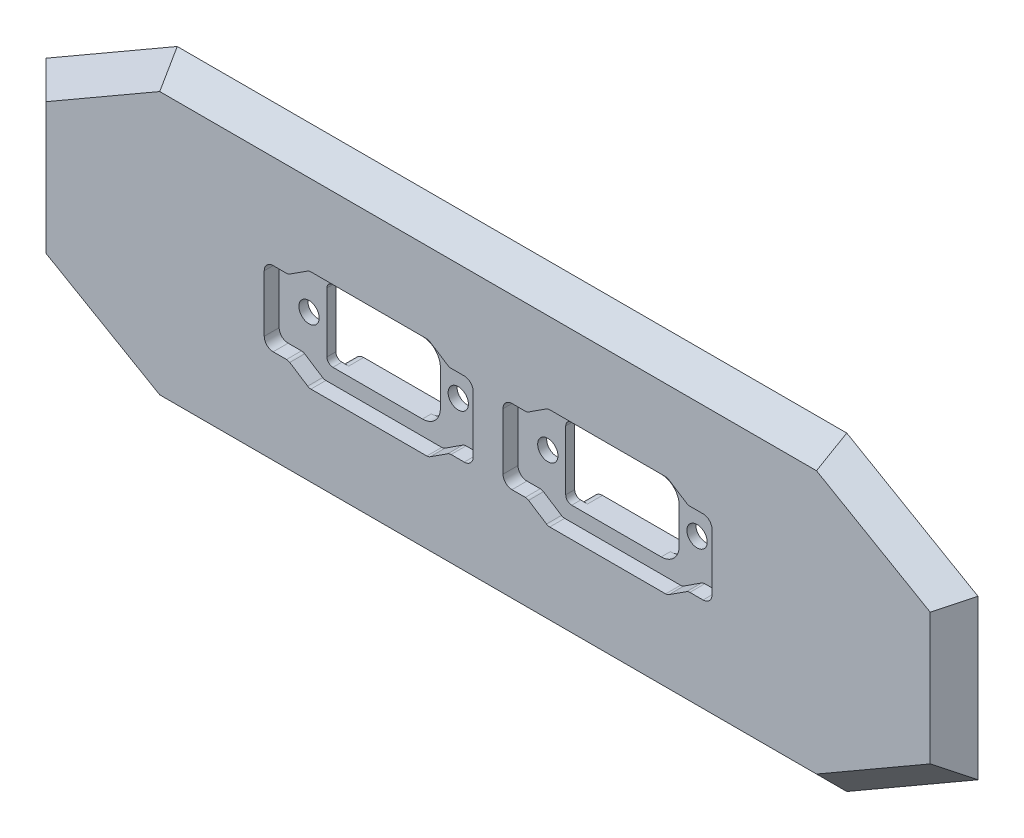
SolidWorks part; units mm, degrees
ref_plane "Płaszczyzna przednia" through (0, 0, 0) normal (0, 0, 1) x (1, 0, 0)
ref_plane "Płaszczyzna górna" through (0, 0, 0) normal (0, 1, 0) x (1, 0, 0)
ref_plane "Płaszczyzna prawa" through (0, 0, 0) normal (1, 0, 0) x (0, 0, -1)
sketch "Sketch1" plane through (0, 0, 0) normal (0, 0, 1) x (1, 0, 0)
  line L0 (0, 0) -> (75, 0) construction
  line L1 (0, 0) -> (40, 0) construction
  line L2 (0, 0) -> (-35, 0) construction
  line L3 (-35, 28) -> (75, 28)
  line L4 (75, -28) -> (-35, -28)
  circle A0 centre (0, 0) radius 28 construction
  arc A1 (75, -28) -> (75, 28) centre (75, 0) ccw
  arc A2 (-35, 28) -> (-35, -28) centre (-35, 0) ccw
  circle A3 centre (40, 0) radius 28 construction
  point P3 (0, 0)
  dimension "D1" = 40
  dimension "D2" = 56
  dimension "D3" = 56
  dimension "D7" = 56
  dimension "D8" = 56
  dimension "D4" = 75
  dimension "D5" = 35
  dimension "D6" = 35
extrude "Boss-Extrude1" add sketch "Sketch1" along normal blind 4
sketch "Sketch2" plane through (0, 0, 0) normal (0, 0, -1) x (-1, 0, 0)
  line L0 (0, 0) -> (0, 6) construction
  line L6 (-7.3485, -6) -> (7.3485, -6)
  line L7 (-10.3923, -6) -> (10.3923, -6) construction
  line L9 (-10.3923, -6) -> (-10.3923, 6) construction
  line L10 (-10.3923, 6) -> (10.3923, 6) construction
  line L11 (10.3923, -6) -> (10.3923, 6) construction
  line L12 (-10.3923, -6) -> (10.3923, 6) construction
  line L13 (-10.3923, 6) -> (10.3923, -6) construction
  line L14 (7.3485, 6) -> (-7.3485, 6)
  line L15 (-40, 0) -> (-40, 6) construction
  line L16 (-47.3485, 6) -> (-32.6515, 6)
  line L17 (-50.3923, -6) -> (-29.6077, -6) construction
  line L18 (-50.3923, -6) -> (-50.3923, 6) construction
  line L19 (-50.3923, 6) -> (-29.6077, 6) construction
  line L20 (-29.6077, -6) -> (-29.6077, 6) construction
  line L21 (-50.3923, -6) -> (-29.6077, 6) construction
  line L22 (-50.3923, 6) -> (-29.6077, -6) construction
  line L23 (-32.6515, -6) -> (-47.3485, -6)
  arc A6 (-8.3983, -8.5714) -> (8.3983, -8.5714) centre (0, 0) ccw
  arc A7 (8.3983, 8.5714) -> (-8.3983, 8.5714) centre (0, 0) ccw
  arc A8 (-8.3983, -8.5714) -> (-7.3485, -6) centre (-7.3485, -7.5) cw
  arc A9 (8.3983, -8.5714) -> (7.3485, -6) centre (7.3485, -7.5) ccw
  arc A10 (8.3983, 8.5714) -> (7.3485, 6) centre (7.3485, 7.5) cw
  arc A11 (-7.3485, 6) -> (-8.3983, 8.5714) centre (-7.3485, 7.5) cw
  arc A12 (-48.3983, -8.5714) -> (-31.6017, -8.5714) centre (-40, 0) ccw
  arc A13 (-31.6017, 8.5714) -> (-48.3983, 8.5714) centre (-40, 0) ccw
  arc A14 (-48.3983, -8.5714) -> (-47.3485, -6) centre (-47.3485, -7.5) cw
  arc A15 (-31.6017, -8.5714) -> (-32.6515, -6) centre (-32.6515, -7.5) ccw
  arc A16 (-31.6017, 8.5714) -> (-32.6515, 6) centre (-32.6515, 7.5) cw
  arc A17 (-47.3485, 6) -> (-48.3983, 8.5714) centre (-47.3485, 7.5) cw
  dimension "D1" = 1.5
  dimension "D2" = 12
  dimension "D5" = 1.5
  dimension "D3" = 20.7846
  dimension "D4" = 6
extrude "Boss-Extrude2" add sketch "Sketch2" along normal blind 2.5
sketch "Sketch3" plane through (0, 0, 4) normal (0, 0, 1) x (1, 0, 0)
  line L0 (0, 8.5) -> (-10, 8.5) construction
  line L1 (-17.5, -6.25) -> (17.5, -6.25) construction
  line L2 (-17.5, -6.25) -> (-17.5, 6.25) construction
  line L3 (-17.5, 6.25) -> (17.5, 6.25) construction
  line L4 (17.5, -6.25) -> (17.5, 6.25) construction
  line L5 (-17.5, -6.25) -> (17.5, 6.25) construction
  line L6 (-17.5, 6.25) -> (17.5, -6.25) construction
  line L7 (-13.5, -8.5) -> (13.5, -8.5) construction
  line L8 (-13.5, -8.5) -> (-13.5, 8.5) construction
  line L9 (-13.5, 8.5) -> (13.5, 8.5) construction
  line L10 (13.5, -8.5) -> (13.5, 8.5) construction
  line L11 (-13.5, -8.5) -> (13.5, 8.5) construction
  line L12 (-13.5, 8.5) -> (13.5, -8.5) construction
  line L13 (0, 8.5) -> (10, 8.5) construction
  line L14 (0, -8.5) -> (-9.9719, -8.5) construction
  line L15 (-9.9719, -8.5) -> (10.0303, -8.5) construction
  line L16 (-17.5, 4.75) -> (-17.5, -4.75)
  line L17 (-16, -6.25) -> (-13.7656, -6.25)
  line L18 (-13.2248, -6.4088) -> (-10.2189, -8.3412)
  line L19 (-9.6782, -8.5) -> (9.7344, -8.5)
  line L20 (10.2785, -8.339) -> (13.2518, -6.411)
  line L21 (13.7959, -6.25) -> (16, -6.25)
  line L22 (17.5, -4.75) -> (17.5, 4.75)
  line L23 (16, 6.25) -> (13.7937, 6.25)
  line L24 (13.2529, 6.4088) -> (10.2471, 8.3412)
  line L25 (9.7063, 8.5) -> (-9.7041, 8.5)
  line L26 (-10.2482, 8.339) -> (-13.2215, 6.411)
  line L27 (-13.7656, 6.25) -> (-16, 6.25)
  line L28 (40, 8.5) -> (30, 8.5) construction
  line L29 (22.5, -6.25) -> (57.5, -6.25) construction
  line L30 (22.5, -6.25) -> (22.5, 6.25) construction
  line L31 (22.5, 6.25) -> (57.5, 6.25) construction
  line L32 (57.5, -6.25) -> (57.5, 6.25) construction
  line L33 (22.5, -6.25) -> (57.5, 6.25) construction
  line L34 (22.5, 6.25) -> (57.5, -6.25) construction
  line L35 (26.5, -8.5) -> (53.5, -8.5) construction
  line L36 (26.5, -8.5) -> (26.5, 8.5) construction
  line L37 (26.5, 8.5) -> (53.5, 8.5) construction
  line L38 (53.5, -8.5) -> (53.5, 8.5) construction
  line L39 (26.5, -8.5) -> (53.5, 8.5) construction
  line L40 (26.5, 8.5) -> (53.5, -8.5) construction
  line L41 (40, 8.5) -> (50, 8.5) construction
  line L42 (40, -8.5) -> (30.0281, -8.5) construction
  line L43 (30.0281, -8.5) -> (50.0303, -8.5) construction
  line L44 (22.5, 4.75) -> (22.5, -4.75)
  line L45 (24, -6.25) -> (26.2344, -6.25)
  line L46 (26.7752, -6.4088) -> (29.7811, -8.3412)
  line L47 (30.3218, -8.5) -> (49.7344, -8.5)
  line L48 (50.2785, -8.339) -> (53.2518, -6.411)
  line L49 (53.7959, -6.25) -> (56, -6.25)
  line L50 (57.5, -4.75) -> (57.5, 4.75)
  line L51 (56, 6.25) -> (53.7937, 6.25)
  line L52 (53.2529, 6.4088) -> (50.2471, 8.3412)
  line L53 (49.7063, 8.5) -> (30.2959, 8.5)
  line L54 (29.7518, 8.339) -> (26.7785, 6.411)
  line L55 (26.2344, 6.25) -> (24, 6.25)
  line L57 (0, 0) -> (40, 0) construction
  arc A0 (17.5, 4.75) -> (16, 6.25) centre (16, 4.75) ccw
  arc A1 (16, -6.25) -> (17.5, -4.75) centre (16, -4.75) ccw
  arc A2 (-17.5, -4.75) -> (-16, -6.25) centre (-16, -4.75) ccw
  arc A3 (-17.5, 4.75) -> (-16, 6.25) centre (-16, 4.75) cw
  arc A4 (-13.2215, 6.411) -> (-13.7656, 6.25) centre (-13.7656, 7.25) cw
  arc A5 (-10.2482, 8.339) -> (-9.7041, 8.5) centre (-9.7041, 7.5) cw
  arc A6 (9.7063, 8.5) -> (10.2471, 8.3412) centre (9.7063, 7.5) cw
  arc A7 (13.7937, 6.25) -> (13.2529, 6.4088) centre (13.7937, 7.25) cw
  arc A8 (13.2518, -6.411) -> (13.7959, -6.25) centre (13.7959, -7.25) cw
  arc A9 (10.2785, -8.339) -> (9.7344, -8.5) centre (9.7344, -7.5) cw
  arc A10 (-10.2189, -8.3412) -> (-9.6782, -8.5) centre (-9.6782, -7.5) ccw
  arc A11 (-13.7656, -6.25) -> (-13.2248, -6.4088) centre (-13.7656, -7.25) cw
  arc A12 (57.5, 4.75) -> (56, 6.25) centre (56, 4.75) ccw
  arc A13 (56, -6.25) -> (57.5, -4.75) centre (56, -4.75) ccw
  arc A14 (22.5, -4.75) -> (24, -6.25) centre (24, -4.75) ccw
  arc A15 (22.5, 4.75) -> (24, 6.25) centre (24, 4.75) cw
  arc A16 (26.7785, 6.411) -> (26.2344, 6.25) centre (26.2344, 7.25) cw
  arc A17 (29.7518, 8.339) -> (30.2959, 8.5) centre (30.2959, 7.5) cw
  arc A18 (49.7063, 8.5) -> (50.2471, 8.3412) centre (49.7063, 7.5) cw
  arc A19 (53.7937, 6.25) -> (53.2529, 6.4088) centre (53.7937, 7.25) cw
  arc A20 (53.2518, -6.411) -> (53.7959, -6.25) centre (53.7959, -7.25) cw
  arc A21 (50.2785, -8.339) -> (49.7344, -8.5) centre (49.7344, -7.5) cw
  arc A22 (29.7811, -8.3412) -> (30.3218, -8.5) centre (30.3218, -7.5) ccw
  arc A23 (26.2344, -6.25) -> (26.7752, -6.4088) centre (26.2344, -7.25) cw
  point P0 (0, 0)
  point P6 (0, 0)
  point P35 (-13.4697, 6.25)
  point P44 (13.5, 6.25)
  point P47 (13.5, -6.25)
  point P56 (-13.4719, -6.25)
  point P57 (40, 0)
  point P62 (40, 0)
  point P111 (0, 0)
  point P112 (0, 0)
  point P113 (0, 0)
  dimension "D7" = 1.5
  dimension "D8" = 1
  dimension "D15" = 1.5
  dimension "D16" = 1
  dimension "D1" = 35
  dimension "D2" = 12.5
  dimension "D3" = 27
  dimension "D4" = 17
  dimension "D5" = 10
  dimension "D6" = 10
  dimension "D9" = 35
  dimension "D10" = 12.5
  dimension "D11" = 27
  dimension "D12" = 17
  dimension "D13" = 10
  dimension "D14" = 10
  dimension "D17" = 40
extrude "Cut-Extrude1" cut sketch "Sketch3" against normal blind 2.5
sketch "Sketch4" plane through (0, 0, -2.5) normal (0, 0, -1) x (-1, 0, 0)
  line L1 (-6.5, -6) -> (8.5, -6)
  line L2 (-9.5, -3) -> (-9.5, 3)
  line L3 (-6.5, 6) -> (8.5, 6)
  line L4 (9.5, -5) -> (9.5, 5)
  line L5 (-9.5, -6) -> (9.5, 6) construction
  line L6 (-9.5, 6) -> (9.5, -6) construction
  line L7 (-46.5, 6) -> (-31.5, 6)
  line L8 (-49.5, 3) -> (-49.5, -3)
  line L9 (-46.5, -6) -> (-31.5, -6)
  line L10 (-30.5, 5) -> (-30.5, -5)
  line L11 (-49.5, 6) -> (-30.5, -6) construction
  line L12 (-49.5, -6) -> (-30.5, 6) construction
  arc A0 (-6.5, -6) -> (-9.5, -3) centre (-6.5, -3) cw
  arc A1 (-9.5, 3) -> (-6.5, 6) centre (-6.5, 3) cw
  arc A2 (8.5, -6) -> (9.5, -5) centre (8.5, -5) ccw
  arc A3 (8.5, 6) -> (9.5, 5) centre (8.5, 5) cw
  arc A4 (-49.5, -3) -> (-46.5, -6) centre (-46.5, -3) ccw
  arc A5 (-46.5, 6) -> (-49.5, 3) centre (-46.5, 3) ccw
  arc A6 (-31.5, -6) -> (-30.5, -5) centre (-31.5, -5) ccw
  arc A7 (-31.5, 6) -> (-30.5, 5) centre (-31.5, 5) cw
  point P0 (0, 0)
  point P18 (-40, 0)
  dimension "D3" = 3
  dimension "D4" = 1
  dimension "D7" = 3
  dimension "D8" = 1
  dimension "D1" = 19
  dimension "D2" = 12
  dimension "D5" = 19
  dimension "D6" = 12
extrude "Cut-Extrude2" cut sketch "Sketch4" against normal through all
sketch "Sketch5" plane through (0, 0, 1.5) normal (0, 0, 1) x (1, 0, 0)
  line L0 (0, 0) -> (12.5, 0) construction
  line L1 (0, 0) -> (-12.5, 0) construction
  line L2 (40, 0) -> (52.5, 0) construction
  line L3 (0, 0) -> (75, 0) construction
  line L4 (40, 0) -> (27.5, 0) construction
  circle A0 centre (-12.5, 0) radius 1.7
  circle A1 centre (12.5, 0) radius 1.7
  circle A3 centre (27.5, 0) radius 1.7
  circle A4 centre (52.5, 0) radius 1.7
  dimension "D1" = 12.5
  dimension "D7" = 3.4
  dimension "D8" = 3.4
  dimension "D9" = 3.4
  dimension "D10" = 3.4
  dimension "D2" = 12.5
  dimension "D3" = 25
  dimension "D4" = 12.5
  dimension "D5" = 12.5
  dimension "D6" = 25
extrude "Cut-Extrude3" cut sketch "Sketch5" against normal through all
sketch "Sketch7" plane through (0, 0, 4) normal (0, 0, 1) x (1, 0, 0)
  line L0 (-35, 22) -> (75, 22)
  line L7 (-35, 22) -> (-54.0526, 11)
  line L8 (-54.0526, 11) -> (-54.0526, -11)
  line L9 (-54.0526, -11) -> (-35, -22)
  line L16 (75, -22) -> (94.0526, -11)
  line L17 (94.0526, -11) -> (94.0526, 11)
  line L18 (94.0526, 11) -> (75, 22)
  line L19 (75, -22) -> (-35, -22)
  line L21 (-15.9474, 11) -> (-35, 22) [skipped]
  line L22 (-35, -22) -> (-15.9474, -11) [skipped]
  line L23 (-15.9474, -11) -> (-15.9474, 11) [skipped]
  line L24 (55.9474, 11) -> (55.9474, -11) [skipped]
  line L25 (55.9474, -11) -> (75, -22) [skipped]
  line L26 (75, 22) -> (55.9474, 11) [skipped]
  circle A0 centre (-35, 0) radius 22 construction
  circle A1 centre (75, 0) radius 22 construction
extrude "Cut-Extrude4" cut sketch "Sketch7" against normal through all draft 45 flip side to cut
sketch "Sketch8" plane through (0, 0, 4) normal (0, 0, 1) x (1, 0, 0)
  point P0 (-12.5, 0)
  point P1 (12.5, 0)
  point P3 (27.5, 0)
  point P5 (52.5, 0)
sketch "Sketch9" plane through (0, 0, 0) normal (0, 0, -1) x (-1, 0, 0)
  point P0 (-52.5, 0)
  point P1 (-27.5, 0)
  point P3 (-12.5, 0)
  point P5 (12.5, 0)
